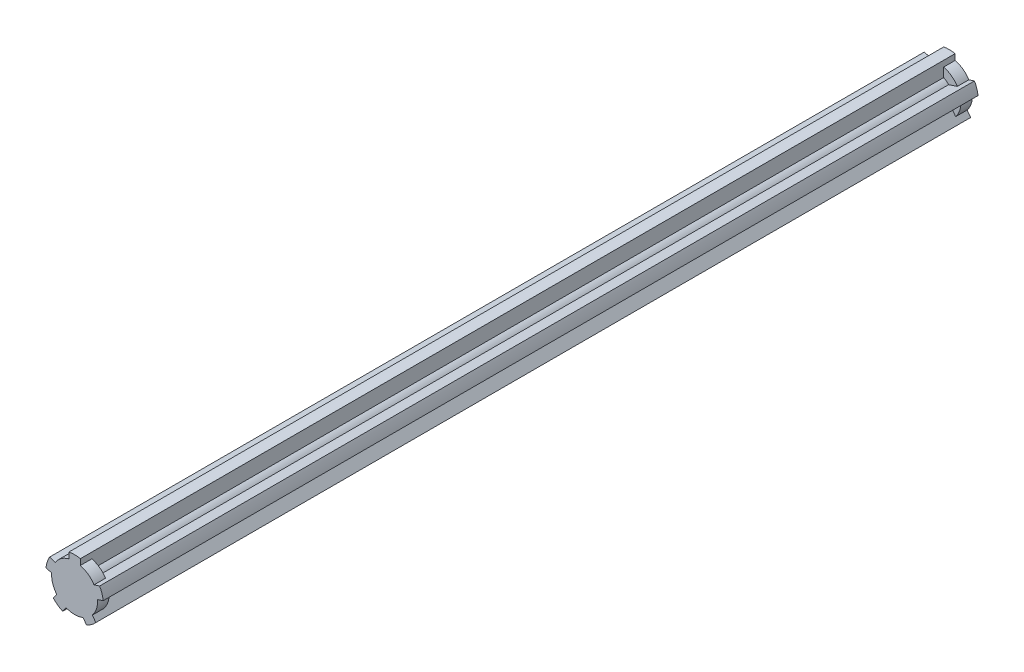
SolidWorks part; units mm, degrees
ref_plane "Front Plane" through (0, 0, 0) normal (0, 0, 1) x (1, 0, 0)
ref_plane "Top Plane" through (0, 0, 0) normal (0, 1, 0) x (1, 0, 0)
ref_plane "Right Plane" through (0, 0, 0) normal (1, 0, 0) x (0, 0, -1)
sketch "Sketch1" plane through (0, 0, 0) normal (0, 0, 1) x (1, 0, 0)
  circle A0 centre (0, 0) radius 3.175
  dimension "D1" = 6.35
extrude "Boss-Extrude1" add sketch "Sketch1" along normal blind 96.52
sketch "Sketch2" plane through (0, 0, 96.52) normal (0, 0, 1) x (1, 0, 0)
  circle A0 centre (0, 0) radius 5.08
  dimension "D1" = 10.16
extrude "Boss-Extrude2" add sketch "Sketch2" against normal blind 2.54
mirror "Mirror1" about plane through (0, 0, 0) normal (0, 0, 1) of "Boss-Extrude2", "Boss-Extrude1"
sketch "Sketch3" plane through (0, 0, -96.52) normal (0, 0, -1) x (-1, 0, 0)
  line L0 (0, 0) -> (0, 5.08) construction
  line L1 (-1.27, 4.9187) -> (-1.27, 2.1997)
  line L2 (1.27, 4.9187) -> (1.27, 2.1997)
  line L3 (-1.27, 2.1997) -> (1.27, 2.1997)
  line L4 (-1.27, 4.9187) -> (-1.27, 6.2217)
  line L5 (1.27, 4.9187) -> (1.27, 6.2217)
  line L6 (1.6996, 1.8876) -> (2.4845, -0.5281)
  line L7 (4.2855, 2.7278) -> (1.6996, 1.8876)
  line L8 (5.0704, 0.3121) -> (2.4845, -0.5281)
  line L9 (5.0704, 0.3121) -> (6.3096, 0.7148)
  line L10 (4.2855, 2.7278) -> (5.5247, 3.1305)
  line L11 (2.3204, -1.0331) -> (0.2655, -2.5261)
  line L12 (3.9186, -3.2328) -> (2.3204, -1.0331)
  line L13 (1.8637, -4.7258) -> (0.2655, -2.5261)
  line L14 (1.8637, -4.7258) -> (2.6296, -5.78)
  line L15 (3.9186, -3.2328) -> (4.6845, -4.287)
  line L16 (-0.2655, -2.5261) -> (-2.3204, -1.0331)
  line L17 (-1.8637, -4.7258) -> (-0.2655, -2.5261)
  line L18 (-3.9186, -3.2328) -> (-2.3204, -1.0331)
  line L19 (-3.9186, -3.2328) -> (-4.6845, -4.287)
  line L20 (-1.8637, -4.7258) -> (-2.6296, -5.78)
  line L21 (-2.4845, -0.5281) -> (-1.6996, 1.8876)
  line L22 (-5.0704, 0.3121) -> (-2.4845, -0.5281)
  line L23 (-4.2855, 2.7278) -> (-1.6996, 1.8876)
  line L24 (-4.2855, 2.7278) -> (-5.5247, 3.1305)
  line L25 (-5.0704, 0.3121) -> (-6.3096, 0.7148)
  circle A0 centre (0, 0) radius 5.08 construction
  arc A1 (-1.27, 6.2217) -> (1.27, 6.2217) centre (0, 0) cw
  circle A2 centre (0, 0) radius 2.54 construction
  arc A3 (5.5247, 3.1305) -> (6.3096, 0.7148) centre (0, 0) cw
  arc A4 (4.6845, -4.287) -> (2.6296, -5.78) centre (0, 0) cw
  arc A5 (-2.6296, -5.78) -> (-4.6845, -4.287) centre (0, 0) cw
  arc A6 (-6.3096, 0.7148) -> (-5.5247, 3.1305) centre (0, 0) cw
  point P39 (0, 0)
  dimension "D1" = 5.08
  dimension "D3" = 6.35
  dimension "D2" = 2.54
  dimension "D4" = 5
extrude "Boss-Extrude3" add sketch "Sketch3" against normal through all
